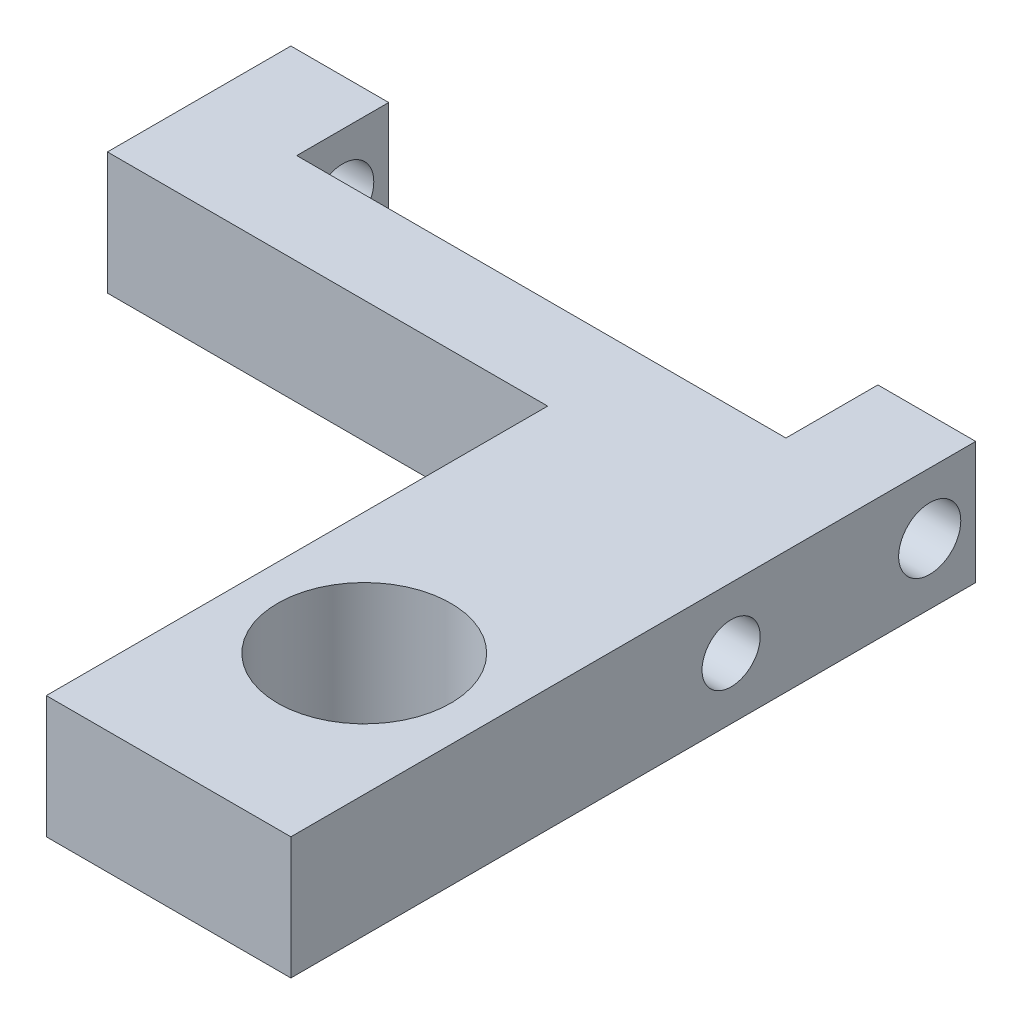
SolidWorks part; units mm, degrees
material "6061 Alloy"
ref_plane "Front Plane" through (0, 0, 0) normal (0, 0, 1) x (1, 0, 0)
ref_plane "Top Plane" through (0, 0, 0) normal (0, 1, 0) x (1, 0, 0)
ref_plane "Right Plane" through (0, 0, 0) normal (1, 0, 0) x (0, 0, -1)
sketch "Sketch1" plane through (0, 0, 0) normal (0, 1, 0) x (1, 0, 0)
  line L1 (-8.89, -8.89) -> (8.89, -8.89)
  line L2 (-8.89, -8.89) -> (-8.89, 8.89)
  line L3 (-8.89, 8.89) -> (8.89, 8.89)
  line L4 (8.89, -8.89) -> (8.89, 8.89)
  line L5 (-8.89, -8.89) -> (8.89, 8.89) construction
  line L6 (-8.89, 8.89) -> (8.89, -8.89) construction
  point P0 (0, 0)
  dimension "D1" = 17.78
  dimension "D2" = 17.78
extrude "Boss-Extrude1" add sketch "Sketch1" along normal blind 3.175
sketch "Sketch2" plane through (0, 3.175, 0) normal (0, 1, 0) x (1, 0, 0)
  line L0 (8.89, 8.89) -> (-8.89, 8.89) construction
  line L1 (-6.35, 11.2776) -> (6.35, 11.2776)
  line L2 (-6.35, 11.2776) -> (-6.35, 6.5024)
  line L3 (-6.35, 6.5024) -> (6.35, 6.5024)
  line L4 (6.35, 11.2776) -> (6.35, 6.5024)
  line L5 (-6.35, 11.2776) -> (6.35, 6.5024) construction
  line L6 (-6.35, 6.5024) -> (6.35, 11.2776) construction
  line L7 (-8.89, 8.89) -> (-8.89, -8.89) construction
  point P0 (0, 8.89)
  dimension "D1" = 2.3876
  dimension "D2" = 2.54
extrude "Cut-Extrude1" cut sketch "Sketch2" against normal through all contours L1 L4 L3 L2
hole_wizard "#8 Clearance Hole1" positions "Sketch6" profile "Sketch7" hole size "#8" standard "ANSI Inch" end condition through all
sketch "Sketch6" plane through (0, 3.175, 0) normal (0, 1, 0) x (1, 0, 0)
  line L0 (8.89, 8.89) -> (6.35, 8.89) construction
  line L2 (8.89, -8.89) -> (8.89, 8.89) construction
  point P0 (5.715, -3.81)
  dimension "D1" = 12.7
  dimension "D2" = 3.175
sketch "Sketch7" plane through (5.715, 3.175, 3.81) normal (1, 0, 0) x (0, 0, 1)
  line L0 (0, 0) -> (0, 3.175)
  line L1 (0, 3.175) -> (2.2479, 3.175)
  line L2 (2.2479, 3.175) -> (2.2479, 0)
  line L5 (2.2479, 0) -> (0, 0)
  line L11 (0, -6.35) -> (0, 107.95) construction
  dimension "Thru Hole Dia." = 4.4958
  dimension "Thru Hole Depth" = 3.175
hole_wizard "#0 Clearance Hole1" positions "Sketch10" profile "Sketch11" hole size "#0" standard "ANSI Inch" end condition through all
sketch "Sketch10" plane through (8.89, 0, 0) normal (1, 0, 0) x (0, 0, -1)
  line L0 (-8.89, 3.175) -> (8.89, 3.175) construction
  line L1 (8.89, 3.175) -> (8.89, 0) construction
  point P0 (7.6962, 1.5875)
  dimension "D1" = 1.5875
  dimension "D2" = 1.1938
sketch "Sketch11" plane through (8.89, 1.5875, -7.6962) normal (0, 1, 0) x (0, 0, -1)
  line L0 (0, 0) -> (0, 17.78)
  line L1 (0, 17.78) -> (0.8064, 17.78)
  line L2 (0.8064, 17.78) -> (0.8064, 0)
  line L5 (0.8064, 0) -> (0, 0)
  line L11 (0, -6.35) -> (0, 107.95) construction
  dimension "Thru Hole Dia." = 1.6129
  dimension "Thru Hole Depth" = 17.78
hole_wizard "#1-72 Tapped Hole1" positions "Sketch14" profile "Sketch15" tap size "#1-72" standard "ANSI Inch" end condition through all
sketch "Sketch14" plane through (8.89, 0, 0) normal (1, 0, 0) x (0, 0, -1)
  line L1 (-8.89, 3.175) -> (8.89, 3.175) construction
  line L2 (8.89, 3.175) -> (8.89, 0) construction
  point P0 (2.54, 1.5875)
  dimension "D1" = 1.5875
  dimension "D2" = 6.35
cosmetic thread "Hole Thread1" parameters "D2"=1.8542
sketch "Sketch15" plane through (8.89, 1.5875, -2.54) normal (0, 1, 0) x (0, 0, -1)
  line L0 (0, 0) -> (0, 17.78)
  line L1 (0, 17.78) -> (0.7556, 17.78)
  line L2 (0.7556, 17.78) -> (0.7556, 0)
  line L5 (0.7556, 0) -> (0, 0)
  line L11 (0, -6.35) -> (0, 107.95) construction
  dimension "Thru Tap Drill Dia." = 1.5113
  dimension "Thru Tap Drill Depth" = 17.78
sketch "Sketch16" plane through (0, 3.175, 0) normal (0, 1, 0) x (1, 0, 0)
  line L0 (-6.35, 8.89) -> (-8.89, 8.89) construction
  line L1 (2.54, 4.1275) -> (-13.2131, 4.1275)
  line L2 (2.54, 4.1275) -> (2.54, -9.4466)
  line L3 (2.54, -9.4466) -> (-13.2131, -9.4466)
  line L4 (-13.2131, 4.1275) -> (-13.2131, -9.4466)
  line L5 (-8.89, 8.89) -> (-8.89, -8.89) construction
  dimension "D1" = 4.7625
  dimension "D2" = 11.43
extrude "Cut-Extrude2" cut sketch "Sketch16" against normal through all
